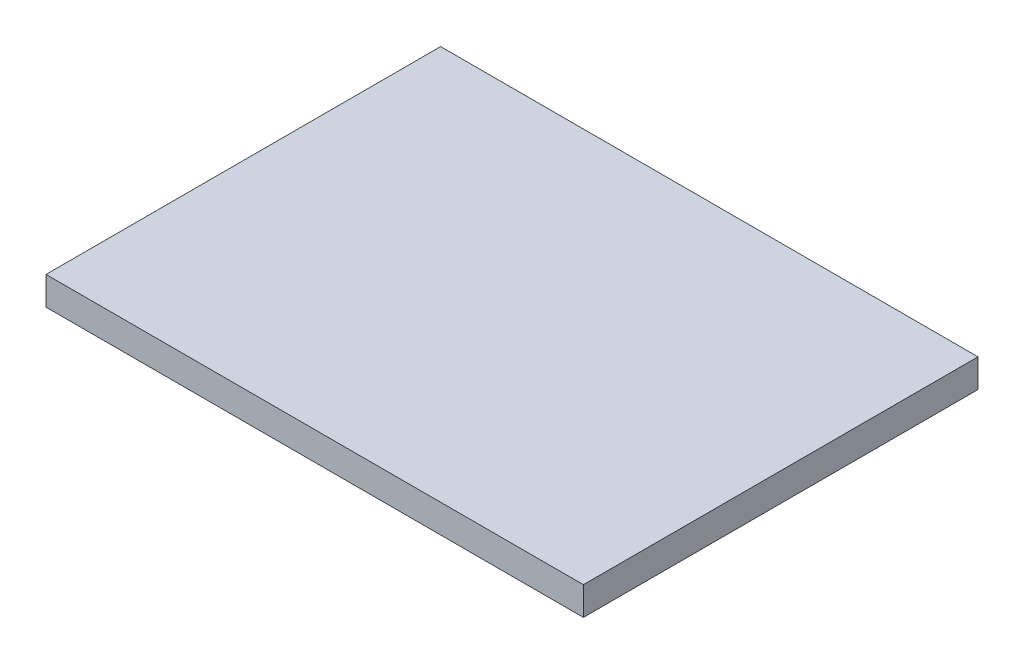
SolidWorks part; units mm, degrees
ref_plane "Front Plane" through (0, 0, 0) normal (0, 0, 1) x (1, 0, 0)
ref_plane "Top Plane" through (0, 0, 0) normal (0, 1, 0) x (1, 0, 0)
ref_plane "Right Plane" through (0, 0, 0) normal (1, 0, 0) x (0, 0, -1)
sketch "Sketch2" plane through (0, 0, 0) normal (0, 1, 0) x (1, 0, 0)
  line L1 (-33.1395, 18.1838) -> (22.7605, 18.1838)
  line L2 (-33.1395, 18.1838) -> (-33.1395, -22.8662)
  line L3 (-33.1395, -22.8662) -> (22.7605, -22.8662)
  line L4 (22.7605, 18.1838) -> (22.7605, -22.8662)
  dimension "D1" = 55.9
  dimension "D2" = 41.05
extrude "Boss-Extrude2" add sketch "Sketch2" along normal blind 2.95
